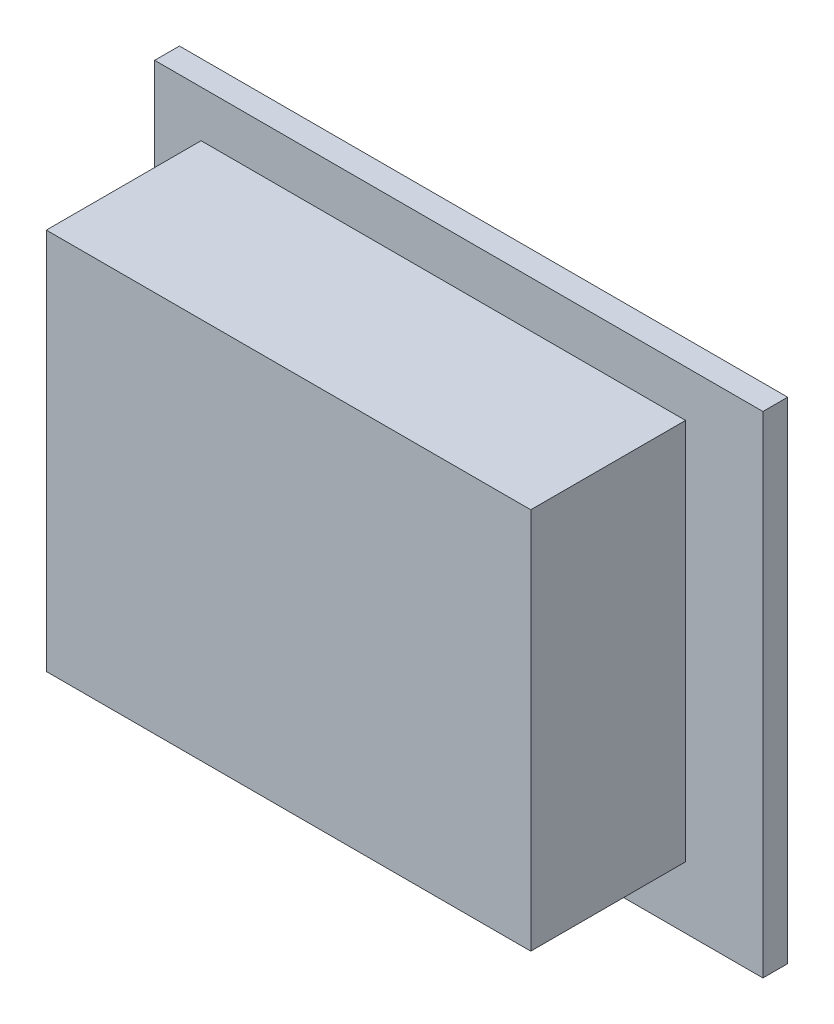
SolidWorks part; units mm, degrees
ref_plane "Plan de face" through (0, 0, 0) normal (0, 0, 1) x (1, 0, 0)
ref_plane "Plan de dessus" through (0, 0, 0) normal (0, 1, 0) x (1, 0, 0)
ref_plane "Plan de droite" through (0, 0, 0) normal (1, 0, 0) x (0, 0, -1)
sketch "Esquisse1" plane through (0, 0, 0) normal (0, 0, 1) x (1, 0, 0)
  line L1 (0, 0) -> (39.3, 0)
  line L2 (0, 0) -> (0, 31.7)
  line L3 (0, 31.7) -> (39.3, 31.7)
  line L4 (39.3, 0) -> (39.3, 31.7)
  dimension "D1" = 39.3
  dimension "D2" = 31.7
extrude "Boss.-Extru.1" add sketch "Esquisse1" along normal blind 1.6
sketch "Esquisse2" plane through (0, 0, 1.6) normal (0, 0, 1) x (1, 0, 0)
  line L1 (3, 4) -> (34.3, 4)
  line L2 (3, 4) -> (3, 28.7)
  line L3 (3, 28.7) -> (34.3, 28.7)
  line L4 (34.3, 4) -> (34.3, 28.7)
  line L5 (0, 31.7) -> (0, 0) construction
  line L6 (0, 0) -> (39.3, 0) construction
  line L7 (39.3, 0) -> (39.3, 31.7) construction
  line L8 (39.3, 31.7) -> (0, 31.7) construction
  point P6 (19.65, 0)
  dimension "D1" = 3
  dimension "D2" = 4
  dimension "D3" = 3
  dimension "5" = 5
extrude "Boss.-Extru.2" add sketch "Esquisse2" along normal blind 10
